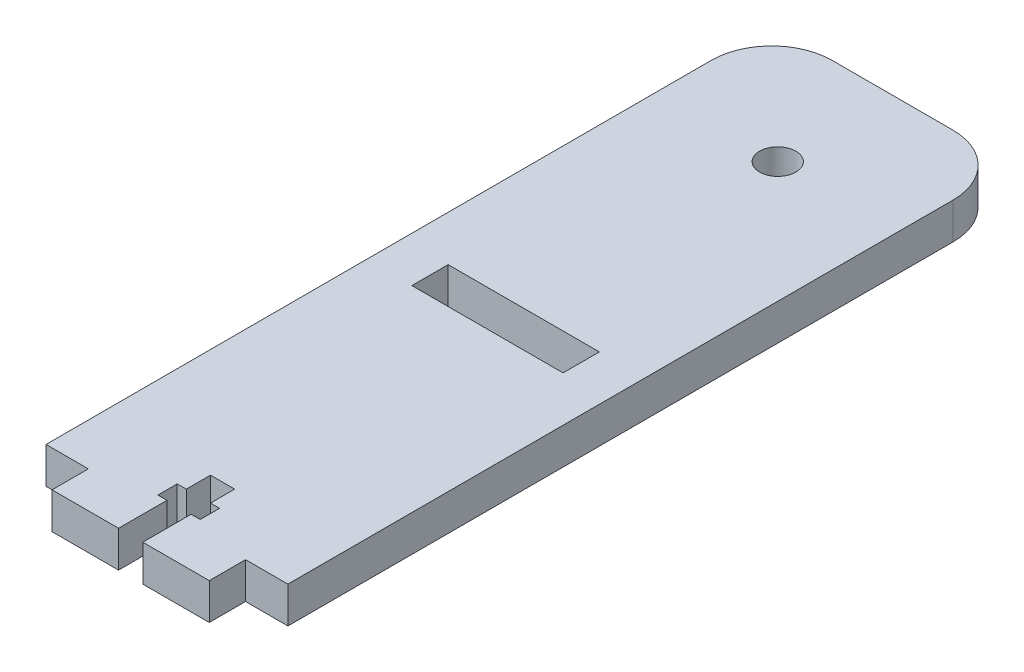
SolidWorks part; units mm, degrees
ref_plane "Front Plane" through (0, 0, 0) normal (0, 0, 1) x (1, 0, 0)
ref_plane "Top Plane" through (0, 0, 0) normal (0, 1, 0) x (1, 0, 0)
ref_plane "Right Plane" through (0, 0, 0) normal (1, 0, 0) x (0, 0, -1)
sketch "Sketch1" plane through (0, 0, 0) normal (0, 1, 0) x (1, 0, 0)
  line L0 (-20, -57.2382) -> (-13, -57.2382) construction
  line L1 (-10, 62.7618) -> (10, 62.7618)
  line L3 (-20, -57.2382) -> (-13, -57.2382)
  line L4 (20, 52.7618) -> (20, -57.2382)
  line L5 (-20, 62.7618) -> (20, -57.2382) construction
  line L6 (-20, -57.2382) -> (20, 62.7618) construction
  line L7 (-13, -57.2382) -> (-13, -63.2382)
  line L8 (-13, -63.2382) -> (-2, -63.2382)
  line L9 (13, -63.2382) -> (13, -57.2382)
  line L10 (-20, 52.7618) -> (-20, -57.2382)
  line L11 (0, 62.7618) -> (0, 43.7618) construction
  line L15 (13, -57.2382) -> (20, -57.2382)
  line L18 (-2, -63.2382) -> (-2, -55.2382)
  line L19 (-2, -55.2382) -> (-3.5, -55.2382)
  line L20 (-3.5, -55.2382) -> (-3.5, -52.0382)
  line L21 (-3.5, -52.0382) -> (-2, -52.0382)
  line L22 (3.5, -52.0382) -> (3.5, -55.2382)
  line L23 (3.5, -55.2382) -> (2, -55.2382)
  line L24 (2, -55.2382) -> (2, -63.2382)
  line L25 (-2, -52.0382) -> (-2, -48.0382)
  line L26 (-2, -48.0382) -> (2, -48.0382)
  line L27 (2, -48.0382) -> (2, -52.0382)
  line L28 (2, -52.0382) -> (3.5, -52.0382)
  line L29 (2, -63.2382) -> (13, -63.2382)
  line L37 (-12.5, 1.7618) -> (12.5, 1.7618)
  line L38 (-12.5, 1.7618) -> (-12.5, -4.2382)
  line L39 (-12.5, -4.2382) -> (12.5, -4.2382)
  line L40 (12.5, 1.7618) -> (12.5, -4.2382)
  line L41 (-12.5, 1.7618) -> (12.5, -4.2382) construction
  line L42 (-12.5, -4.2382) -> (12.5, 1.7618) construction
  arc A0 (10, 62.7618) -> (20, 52.7618) centre (10, 52.7618) cw
  arc A1 (-10, 62.7618) -> (-20, 52.7618) centre (-10, 52.7618) ccw
  circle A3 centre (0, 43.7618) radius 3
  point P0 (0, 2.7618)
  point P15 (0, -1.2382)
  dimension "D17" = 10
  dimension "D2" = 120
  dimension "D3" = 40
  dimension "D4" = 7
  dimension "D5" = 6
  dimension "D6" = 26
  dimension "D7" = 4
  dimension "D8" = 11
  dimension "D9" = 8
  dimension "D10" = 3.2
  dimension "D11" = 4
  dimension "D12" = 1.5
  dimension "D13" = 19
  dimension "D14" = 110
  dimension "D15" = 25
  dimension "D16" = 6
  dimension "D18" = 64
extrude "Boss-Extrude1" add sketch "Sketch1" along normal blind 6
